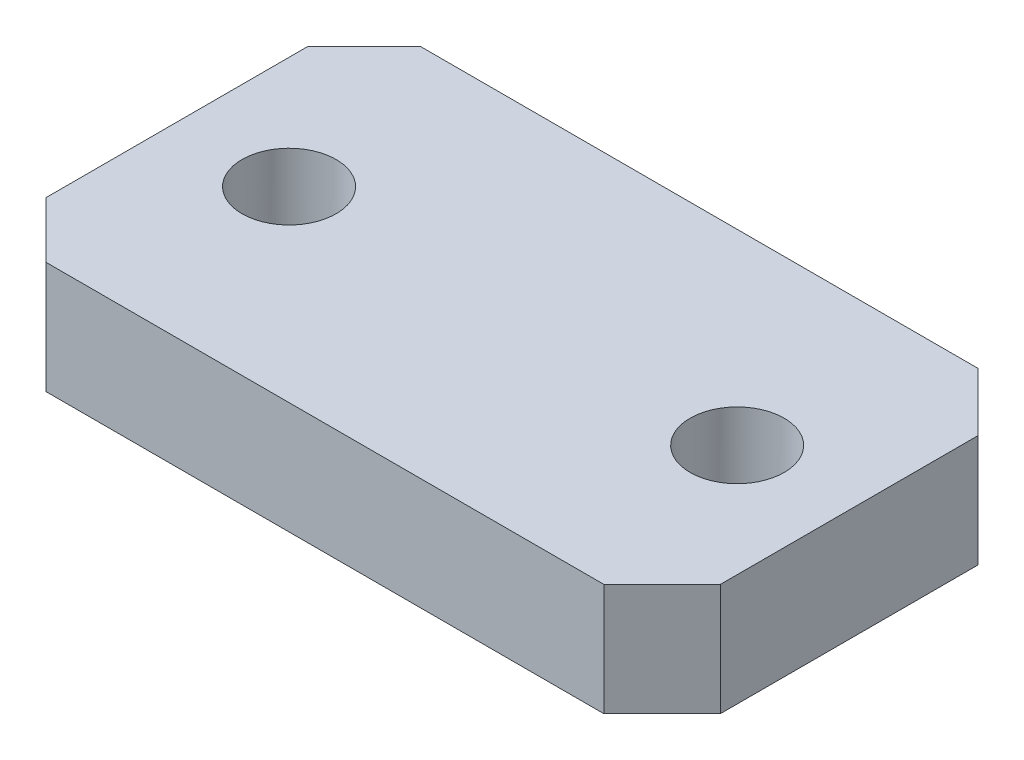
SolidWorks part; units mm, degrees
ref_plane "Front Plane" through (0, 0, 0) normal (0, 0, 1) x (1, 0, 0)
ref_plane "Top Plane" through (0, 0, 0) normal (0, 1, 0) x (1, 0, 0)
ref_plane "Right Plane" through (0, 0, 0) normal (1, 0, 0) x (0, 0, -1)
sketch "Sketch1" plane through (0, 0, 0) normal (0, 1, 0) x (1, 0, 0)
  line L1 (-19.05, -10.6045) -> (19.05, -10.6045)
  line L2 (-19.05, -10.6045) -> (-19.05, 10.6045)
  line L3 (-19.05, 10.6045) -> (19.05, 10.6045)
  line L4 (19.05, -10.6045) -> (19.05, 10.6045)
  line L5 (-19.05, -10.6045) -> (19.05, 10.6045) construction
  line L6 (-19.05, 10.6045) -> (19.05, -10.6045) construction
  point P0 (0, 0)
extrude "Boss-Extrude1" add sketch "Sketch1" along normal blind 6.35
sketch "Sketch2" plane through (0, 6.35, 0) normal (0, 1, 0) x (1, 0, 0)
  line L3 (0, 0) -> (-12.7, 0)
  line L4 (0, 0) -> (12.7, 0)
  circle A0 centre (-12.7, 0) radius 2.667
  circle A3 centre (12.7, 0) radius 2.667
  dimension "D1" = 12.7
  dimension "D2" = 12.7
extrude "Cut-Extrude1" cut sketch "Sketch2" against normal blind 9.525
sketch "Sketch3" plane through (0, 6.35, 0) normal (0, 1, 0) x (1, 0, 0)
  line L0 (-19.05, 10.6045) -> (-15.875, 10.6045)
  line L1 (19.05, 10.6045) -> (-19.05, 10.6045) construction
  line L2 (-15.875, 10.6045) -> (-19.05, 7.4295)
  line L3 (-19.05, 10.6045) -> (-19.05, -10.6045) construction
  line L4 (-19.05, 7.4295) -> (-19.05, 10.6045)
  line L5 (19.05, 10.6045) -> (15.748, 10.6045)
  line L6 (15.748, 10.6045) -> (19.05, 7.3025)
  line L7 (19.05, -10.6045) -> (19.05, 10.6045) construction
  line L8 (19.05, 7.3025) -> (19.05, 10.6045)
  line L9 (19.05, -10.6045) -> (15.748, -10.6045)
  line L10 (-19.05, -10.6045) -> (19.05, -10.6045) construction
  line L11 (15.748, -10.6045) -> (19.05, -7.3025)
  line L12 (19.05, -7.3025) -> (19.05, -10.6045)
  line L13 (-19.05, -10.6045) -> (-15.875, -10.6045)
  line L14 (-15.875, -10.6045) -> (-19.05, -7.4295)
  line L15 (-19.05, -7.4295) -> (-19.05, -10.6045)
  dimension "D1" = 3.175
  dimension "D2" = 3.302
extrude "Cut-Extrude2" cut sketch "Sketch3" against normal blind 9.525
